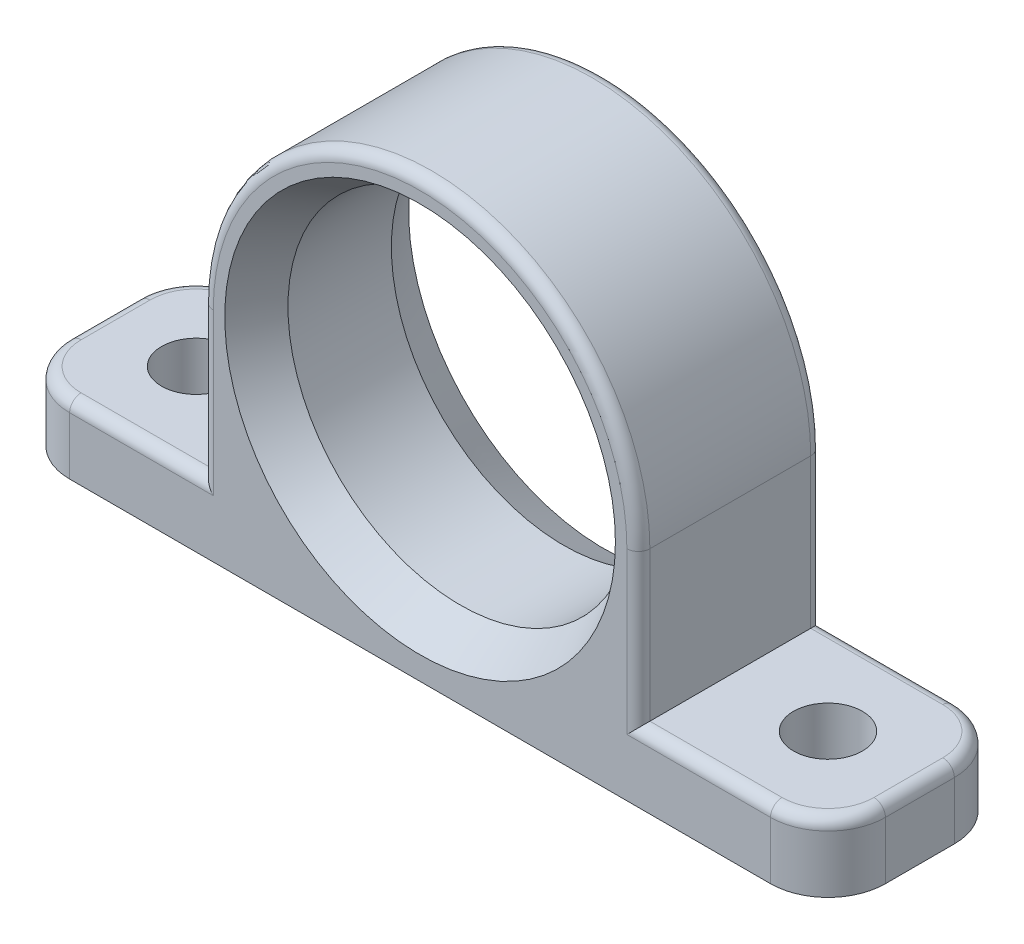
SolidWorks part; units mm, degrees
material "Gray Cast Iron"
ref_plane "Ön Düzlem" through (0, 0, 0) normal (0, 0, 1) x (1, 0, 0)
ref_plane "Üst Düzlem" through (0, 0, 0) normal (0, 1, 0) x (1, 0, 0)
ref_plane "Sağ Düzlem" through (0, 0, 0) normal (1, 0, 0) x (0, 0, -1)
sketch "Sketch1" plane through (0, 0, 0) normal (0, 0, 1) x (1, 0, 0)
  line L0 (-35.5, 0) -> (35.5, 0)
  line L1 (35.5, 0) -> (35.5, 6)
  line L2 (35.5, 6) -> (19, 6)
  line L3 (19, 19) -> (19, 6)
  line L4 (0, 19) -> (0, 0) construction
  line L5 (-19, 19) -> (-19, 6)
  line L6 (-35.5, 6) -> (-19, 6)
  line L7 (-35.5, 0) -> (-35.5, 6)
  arc A0 (19, 19) -> (-19, 19) centre (0, 19) ccw
  circle A1 centre (0, 19) radius 15
  dimension "D3" = 38
  dimension "D5" = 30
  dimension "D1" = 35.5
  dimension "D2" = 19
  dimension "D4" = 6
extrude "Boss-Extrude1" add sketch "Sketch1" along normal blind 16
fillet "Fillet1" radius 5 4 edges at (-35.5, 3, 0) (-35.5, 3, 16) (35.5, 3, 0) (35.5, 3, 16)
sketch "Sketch2" plane through (0, 6, 0) normal (0, 1, 0) x (1, 0, 0)
  line L0 (-19, -16) -> (-30.5, -16) construction
  line L1 (-35.5, -11) -> (-35.5, -5) construction
  line L2 (35.5, -11) -> (35.5, -5) construction
  circle A0 centre (-27.5, -8) radius 3
  circle A1 centre (27.5, -8) radius 3
  dimension "D1" = 6
  dimension "D2" = 8
  dimension "D3" = 8
  dimension "D4" = 8
extrude "Cut-Extrude1" cut sketch "Sketch2" against normal through all both
chamfer "Chamfer1" distance 2 distance2 3.5 1 edges at (15, 19, 16)
chamfer "Chamfer2" distance 3.5 distance2 2 1 edges at (15, 19, 0)
fillet "Fillet2" radius 1 16 edges at (19, 12.5, 16) (0, 38, 16) (-19, 12.5, 16) (24.75, 6, 16) (34.0355, 6, 14.5355) (35.5, 6, 8) (34.0355, 6, 1.4645) (19, 12.5, 0) (-19, 12.5, 0) (-24.75, 6, 16) (-34.0355, 6, 14.5355) (-35.5, 6, 8) (-34.0355, 6, 1.4645) (-24.75, 6, 0) (24.75, 6, 0) (0, 38, 0)
